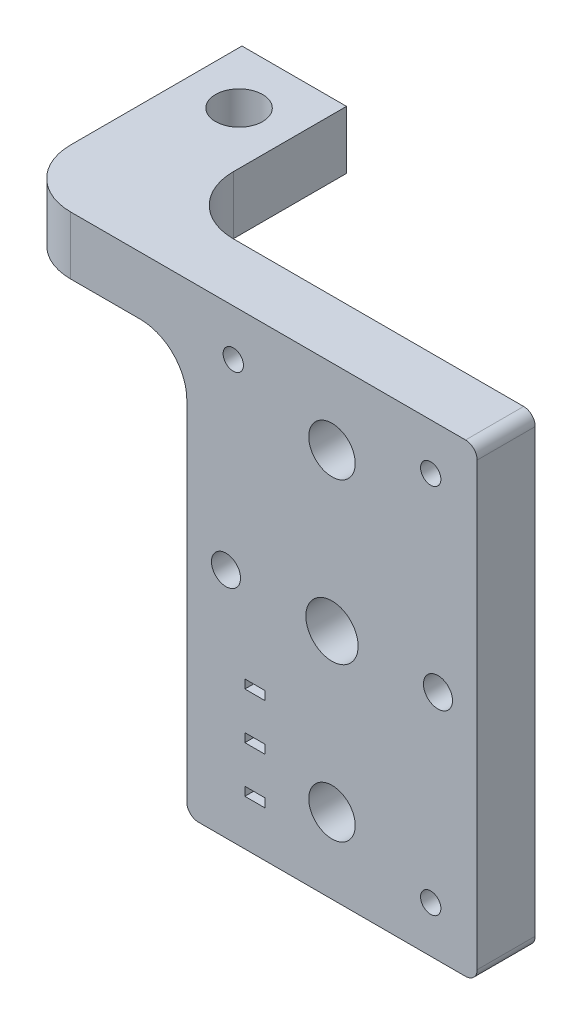
SolidWorks part; units mm, degrees
ref_plane "Plano frontal" through (0, 0, 0) normal (0, 0, 1) x (1, 0, 0)
ref_plane "Plano superior" through (0, 0, 0) normal (0, 1, 0) x (1, 0, 0)
ref_plane "Plano direito" through (0, 0, 0) normal (1, 0, 0) x (0, 0, -1)
sketch "Esboço1" plane through (0, 0, 0) normal (0, 0, 1) x (1, 0, 0)
  line L1 (-25, 40) -> (25, 40)
  line L2 (-25, 40) -> (-25, -40)
  line L3 (-25, -40) -> (25, -40)
  line L4 (25, 40) -> (25, -40)
  line L5 (-25, 40) -> (25, -40) construction
  line L6 (-25, -40) -> (25, 40) construction
  point P0 (0, 0)
  dimension "D1" = 80
  dimension "D2" = 50
extrude "Ressalto-extrusão1" add sketch "Esboço1" along normal mid plane 10
sketch "Esboço2" plane through (0, 0, 5) normal (0, 0, 1) x (1, 0, 0)
  circle A0 centre (0, 0) radius 4.5
  circle A1 centre (0, 27) radius 4
  circle A2 centre (0, -27) radius 4
  circle A3 centre (18.25, 0) radius 2.5
  circle A4 centre (-18.25, 0) radius 2.5
  dimension "D1" = 9
  dimension "D2" = 8
  dimension "D3" = 5
  dimension "D4" = 5
  dimension "D5" = 8
  dimension "D6" = 18.25
  dimension "D7" = 18.25
  dimension "D8" = 27
  dimension "D9" = 27
extrude "Corte-extrusão1" cut sketch "Esboço2" against normal blind 10
sketch "Esboço3" plane through (0, 0, 5) normal (0, 0, 1) x (1, 0, 0)
  line L0 (-25, -40) -> (25, -40) construction
  line L1 (-15, -30.64) -> (-11.5, -30.64)
  line L2 (-15, -30.64) -> (-15, -32.14)
  line L3 (-15, -32.14) -> (-11.5, -32.14)
  line L4 (-11.5, -30.64) -> (-11.5, -32.14)
  line L5 (-15, -30.64) -> (-11.5, -32.14) construction
  line L6 (-15, -32.14) -> (-11.5, -30.64) construction
  line L7 (-15, -22.64) -> (-11.5, -22.64)
  line L8 (-15, -22.64) -> (-15, -24.14)
  line L9 (-15, -24.14) -> (-11.5, -24.14)
  line L10 (-11.5, -22.64) -> (-11.5, -24.14)
  line L11 (-15, -22.64) -> (-11.5, -24.14) construction
  line L12 (-15, -24.14) -> (-11.5, -22.64) construction
  line L13 (-15, -14.64) -> (-11.5, -14.64)
  line L14 (-15, -14.64) -> (-15, -16.14)
  line L15 (-15, -16.14) -> (-11.5, -16.14)
  line L16 (-11.5, -14.64) -> (-11.5, -16.14)
  line L17 (-15, -14.64) -> (-11.5, -16.14) construction
  line L18 (-15, -16.14) -> (-11.5, -14.64) construction
  line L19 (-25, 40) -> (-25, -40) construction
  point P0 (-13.25, -31.39)
  point P5 (-13.25, -23.39)
  point P10 (-13.25, -15.39)
  point P17 (-15, -31.39)
  dimension "D1" = 3.5
  dimension "D2" = 1.5
  dimension "D3" = 3.5
  dimension "D4" = 1.5
  dimension "D5" = 3.5
  dimension "D6" = 1.5
  dimension "D7" = 7.86
  dimension "D8" = 6.5
  dimension "D9" = 6.5
  dimension "D10" = 10
  dimension "D11" = 10
  dimension "D12" = 10
extrude "Corte-extrusão2" cut sketch "Esboço3" against normal blind 22
sketch "Esboço4" plane through (0, 0, 5) normal (0, 0, 1) x (1, 0, 0)
  circle A0 centre (-17, 32) radius 1.75
  circle A1 centre (17, 32) radius 1.75
  circle A2 centre (17, -32) radius 1.75
  circle A3 centre (0, 0) radius 4.5 construction
  dimension "D1" = 3.5
  dimension "D2" = 3.5
  dimension "D3" = 3.5
  dimension "D4" = 34
  dimension "D5" = 64
  dimension "D7" = 17
  dimension "D8" = 64
  dimension "D6" = 32
  dimension "D9" = 17
extrude "Corte-extrusão3" cut sketch "Esboço4" against normal blind 10
sketch "Esboço5" plane through (0, 0, 5) normal (0, 0, 1) x (1, 0, 0)
  line L1 (-17.25, -13.3433) -> (-9.25, -13.3433)
  line L2 (-17.25, -13.3433) -> (-17.25, -33.3433)
  line L3 (-17.25, -33.3433) -> (-9.25, -33.3433)
  line L4 (-9.25, -13.3433) -> (-9.25, -33.3433)
  line L5 (-17.25, -13.3433) -> (-9.25, -33.3433) construction
  line L6 (-17.25, -33.3433) -> (-9.25, -13.3433) construction
  line L8 (25, -40) -> (25, 40) construction
  line L10 (25, 40) -> (-25, 40) construction
  point P0 (-13.25, -23.3433)
  point P5 (-13.25, -33.3433)
  dimension "D1" = 8
  dimension "D2" = 20
  dimension "D3" = 38.25
  dimension "D4" = 63.3433
fillet "Filete1" radius 2 3 edges at (25, 40, 0) (25, -40, 0) (-25, -40, 0)
sketch "Esboço6" plane through (0, 0, -5) normal (0, 0, -1) x (-1, 0, 0)
  line L1 (25, 40) -> (55, 40)
  line L2 (25, 40) -> (25, 30)
  line L3 (25, 30) -> (55, 30)
  line L4 (55, 40) -> (55, 30)
  dimension "D1" = 10
  dimension "D2" = 30
extrude "Ressalto-extrusão2" add sketch "Esboço6" along normal blind 29.5 and the other way blind 10
sketch "Esboço7" plane through (0, 40, 0) normal (0, 1, 0) x (1, 0, 0)
  line L0 (23, 5) -> (-25, 5) construction
  line L1 (-25, 5) -> (-25, 34.5) construction
  circle A0 centre (-46, 25) radius 4.05
  dimension "D1" = 8.1
  dimension "D2" = 20
  dimension "D3" = 21
extrude "Corte-extrusão4" cut sketch "Esboço7" against normal blind 50
sketch "Esboço8" plane through (0, 40, 0) normal (0, 1, 0) x (1, 0, 0)
  line L0 (-55, 34.5) -> (-25, 34.5) construction
  line L1 (-25, 5) -> (-37, 5)
  line L2 (-25, 5) -> (-25, 34.5)
  line L3 (-25, 34.5) -> (-37, 34.5)
  line L4 (-37, 5) -> (-37, 34.5)
  circle A0 centre (-46, 25) radius 4.05 construction
  dimension "D1" = 9
extrude "Corte-extrusão5" cut sketch "Esboço8" against normal blind 50
fillet "Filete2" radius 10 2 edges at (-55, 35, 5) (-37, 35, -5)
fillet "Filete3" radius 8 1 edges at (-25, 30, 0)
